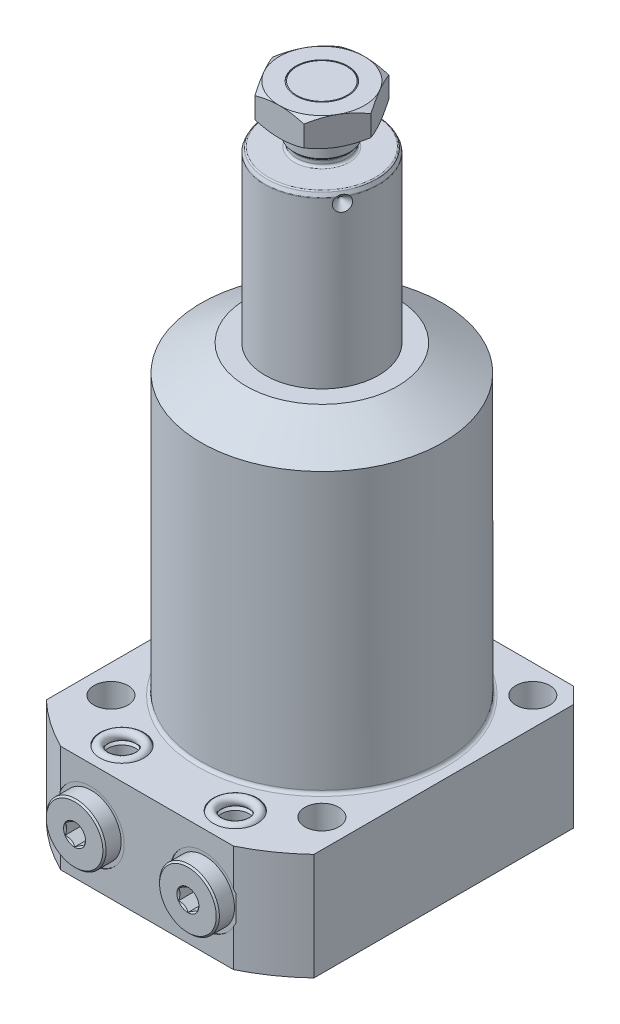
SolidWorks part; units mm, degrees
material "AISI 1020"
ref_plane "Front Plane" through (0, 0, 0) normal (0, 0, 1) x (1, 0, 0)
ref_plane "Top Plane" through (0, 0, 0) normal (0, 1, 0) x (1, 0, 0)
ref_plane "Right Plane" through (0, 0, 0) normal (1, 0, 0) x (0, 0, -1)
sketch "Sketch1" plane through (0, 0, 0) normal (0, 0, 1) x (1, 0, 0)
  line L0 (18, 0) -> (18, 149.5)
  line L1 (18, 149.5) -> (17.3005, 151)
  line L2 (17.3005, 151) -> (8, 151)
  line L3 (8, 151) -> (8, 153)
  line L4 (8, 153) -> (8.935, 153.935)
  line L5 (8.935, 153.935) -> (8.935, 168)
  line L6 (8.935, 168) -> (7.935, 169)
  line L7 (7.935, 169) -> (0, 169)
  line L8 (0, -3.075) -> (0, 64.575) construction
  line L9 (18, 0) -> (0, 0)
  line L10 (0, 0) -> (0, 169)
  line L11 (-30.3581, -34) -> (47.7767, -34) construction
  dimension "D1" = 18
  dimension "D2" = 36
  dimension "D3" = 16
  dimension "D4" = 17.87
  dimension "D5" = 203
  dimension "D6" = 25
  dimension "D7" = 1.5
  dimension "D8" = 45
  dimension "D9" = 1
  dimension "D10" = 15.065
  dimension "D11" = 7.935
  dimension "D12" = 34
revolve "Revolve2" add sketch "Sketch1" angle 360 about L8
fillet "Fillet2" radius 0.75 2 edges at (0, 151, -8) (0, 153, -8)
fillet "Fillet3" radius 0.5 2 edges at (0, 149.5, -18) (0, 151, -17.3005)
sketch "Sketch2" plane through (0, 0, 0) normal (1, 0, 0) x (0, 0, -1)
  line L0 (15.5, 147.67) -> (18, 145.17)
  line L1 (4.2016, 147.67) -> (7.575, 147.67) construction
  line L2 (16.982, 151) -> (-16.982, 151) construction
  line L3 (18, 145.17) -> (18, 147.67)
  line L4 (18, 147.67) -> (15.5, 147.67)
  line L5 (18, 0) -> (18, 149.3892) construction
  dimension "D1" = 3.33
  dimension "D2" = 45
  dimension "D3" = 5
revolve "Cut-Revolve1" cut sketch "Sketch2" angle 360 about L1
sketch "Sketch3" plane through (0, 169, 0) normal (0, 1, 0) x (1, 0, 0)
  line L1 (15.5885, 0) -> (7.7942, 13.5)
  line L2 (7.7942, 13.5) -> (-7.7942, 13.5)
  line L3 (-7.7942, 13.5) -> (-15.5885, 0)
  line L4 (-15.5885, 0) -> (-7.7942, -13.5)
  line L5 (-7.7942, -13.5) -> (7.7942, -13.5)
  line L6 (7.7942, -13.5) -> (15.5885, 0)
  circle A0 centre (0, 0) radius 13.5 construction
  circle A1 centre (0, 0) radius 8.25
  dimension "D2" = 16.5
  dimension "D1" = 27
extrude "Extrude3" add sketch "Sketch3" against normal blind 9
pattern_circular "CirPattern1" count 3 over 360 about axis through (0, -3.075, 0) along (0, -1, 0) of "Cut-Revolve1"
sketch "Sketch4" plane through (0, 0, 0) normal (1, 0, 0) x (0, 0, -1)
  line L0 (13.5, 169) -> (16.5, 169)
  line L1 (16.5, 169) -> (16.5, 167.2679)
  line L2 (16.5, 167.2679) -> (13.5, 169)
  line L3 (13.5, 164.5) -> (-10.9636, 164.5) construction
  line L4 (13.5, 160) -> (13.5, 169) construction
  line L5 (16.5, 161.7321) -> (13.5, 160)
  line L6 (16.5, 160) -> (16.5, 161.7321)
  line L7 (13.5, 160) -> (16.5, 160)
  dimension "D1" = 30
  dimension "D2" = 3
revolve "Cut-Revolve3" cut sketch "Sketch4" angle 360 about axis through (0, -3.075, 0) along (0, -1, 0)
sketch "Sketch6" plane through (0, 0, 0) normal (0, 0, 1) x (1, 0, 0)
  line L0 (0, 0) -> (0, 71.3762) construction
  line L1 (0, 97) -> (24, 97)
  line L2 (24, 97) -> (38.385, 88.6948)
  line L3 (38.385, 88.6948) -> (38.385, 0)
  line L4 (38.385, 0) -> (61.915, 0)
  line L5 (61.915, 0) -> (61.915, -34)
  line L6 (61.915, -34) -> (0, -34)
  line L7 (0, -34) -> (0, 97)
  dimension "D1" = 123.83
  dimension "D2" = 131
  dimension "D3" = 34
  dimension "D4" = 76.77
  dimension "D5" = 30
  dimension "D6" = 48
revolve "Revolve3" add sketch "Sketch6" angle 360 about L0
sketch "Sketch7" plane through (0, 0, 0) normal (0, 1, 0) x (-1, 0, 0)
  line L0 (0, 0) -> (0, -52.3237) construction
  line L1 (-42.5, 55.5) -> (42.5, 55.5)
  line L2 (-42.5, 55.5) -> (-42.5, -42.5)
  line L3 (-42.5, -42.5) -> (42.5, -42.5)
  line L4 (42.5, 55.5) -> (42.5, -42.5)
  dimension "D1" = 85
  dimension "D2" = 98
  dimension "D3" = 42.5
extrude "Cut-Extrude5" cut sketch "Sketch7" against normal through all flip side to cut
sketch "Sketch8" plane through (0, 0, 0) normal (0, 1, 0) x (-1, 0, 0)
  circle A0 centre (-33.5, 33.5) radius 5.4
  dimension "D1" = 10.8
  dimension "D2" = 33.5
  dimension "D3" = 33.5
extrude "Cut-Extrude6" cut sketch "Sketch8" against normal through all
pattern_circular "CirPattern2" count 4 over 360 about axis through (0, 0, 0) along (0, 1, 0) of "Cut-Extrude6"
chamfer "Chamfer1" distance 5 angle 45 2 edges at (-42.5, -17, -42.5) (42.5, -17, -42.5)
fillet "Fillet5" radius 1 1 edges at (0, 0, -38.385)
ref_plane "Plane1" through (0, -17, 0) normal (0, 1, 0) x (-1, 0, 0)
sketch "Sketch11" plane through (0, -17, 0) normal (0, 1, 0) x (-1, 0, 0)
  line L0 (-18, 42.9716) -> (-18, 19.7499) construction
  line L1 (-28.75, 55.5) -> (-28.75, 55.25)
  line L2 (27.4448, 55.5) -> (-27.4448, 55.5) construction
  line L3 (-28.75, 55.25) -> (-24.65, 55.25)
  line L4 (-24.65, 55.25) -> (-23.945, 54.545)
  line L5 (-23.945, 54.545) -> (-23.945, 36.53)
  line L6 (-23.945, 36.53) -> (-18, 36.53)
  line L7 (-18, 36.53) -> (-18, 55.5)
  line L8 (-18, 55.5) -> (-28.75, 55.5)
  dimension "D1" = 18
  dimension "D2" = 0.25
  dimension "D3" = 11.89
  dimension "D4" = 18.72
  dimension "D5" = 21.5
  dimension "D6" = 45
  dimension "D7" = 0.705
revolve "Cut-Revolve5" cut sketch "Sketch11" angle 360 about L0
ref_plane "Plane2" through (0, 0, 45.5) normal (0, 0, 1) x (1, 0, 0)
sketch "Sketch13" plane through (0, 0, 45.5) normal (0, 0, 1) x (1, 0, 0)
  line L0 (-22.375, -22) -> (-22.375, -31)
  line L1 (-22.375, -31) -> (-23.125, -31.75)
  line L2 (-23.125, -31.75) -> (-25, -31.75)
  line L3 (-25, -31.75) -> (-25, -34)
  line L5 (-25, -34) -> (-18, -34)
  line L6 (-18, -34) -> (-18, -22)
  line L7 (-18, -22) -> (-22.375, -22)
  line L8 (-18, 15.2099) -> (-18, -4.3918) construction
  line L9 (-27.4448, -34) -> (27.4448, -34) construction
  dimension "D1" = 18
  dimension "D2" = 8.75
  dimension "D3" = 12
  dimension "D4" = 2.25
  dimension "D5" = 14
  dimension "D6" = 45
  dimension "D7" = 0.75
revolve "Cut-Revolve6" cut sketch "Sketch13" angle 360 about L8
mirror "Mirror4" about plane through (0, -17, 0) normal (0, 1, 0) of "Cut-Revolve6"
sketch "Sketch14" plane through (0, -17, 0) normal (0, 1, 0) x (-1, 0, 0)
  line L0 (-18, 32.5881) -> (-18, 43.3353) construction
  line L1 (-18, 36.53) -> (-18, 54.545) construction
  line L2 (-21.5, 60.55) -> (-27, 60.55)
  line L3 (-27, 60.55) -> (-27.5, 60.05)
  line L4 (-27.5, 60.05) -> (-27.5, 55.25)
  line L5 (-7.25, 55.25) -> (-27.9447, 55.25) construction
  line L6 (-27.5, 55.25) -> (-23.6, 55.25)
  line L7 (-11.35, 55.25) -> (-24.65, 55.25) construction
  line L8 (-23.6, 55.25) -> (-23.6, 52.7474)
  line L9 (-23.6, 52.7474) -> (-18, 52.7474)
  line L10 (-18, 52.7474) -> (-18, 52.7484)
  line L11 (-18, 52.7484) -> (-21, 54.551)
  line L12 (-21, 54.551) -> (-21, 60.05)
  line L13 (-21, 60.05) -> (-21.5, 60.55)
  dimension "D1" = 11.2
  dimension "D2" = 2.5026
  dimension "D3" = 59
  dimension "D4" = 6
  dimension "D5" = 5.3
  dimension "D6" = 19
  dimension "D7" = 45
  dimension "D8" = 0.5
  dimension "D9" = 45
  dimension "D10" = 0.5
  dimension "D11" = 0.001
revolve "Revolve6" add sketch "Sketch14" angle 360 about L0
sketch "Sketch15" plane through (0, 0, 60.55) normal (0, 0, 1) x (1, 0, 0)
  line L1 (21, -18.7321) -> (21, -15.2679)
  line L2 (21, -15.2679) -> (18, -13.5359)
  line L3 (18, -13.5359) -> (15, -15.2679)
  line L4 (15, -15.2679) -> (15, -18.7321)
  line L5 (15, -18.7321) -> (18, -20.4641)
  line L6 (18, -20.4641) -> (21, -18.7321)
  circle A0 centre (18, -17) radius 3 construction
  dimension "D1" = 6
extrude "Cut-Extrude8" cut sketch "Sketch15" against normal blind 5.3
mirror "Mirror1" about plane through (0, 0, 0) normal (1, 0, 0) of "Mirror4", "Cut-Extrude8", "Revolve6", "Cut-Revolve6", "Cut-Revolve5"
sketch "Sketch16" plane through (0, 0, 45.5) normal (0, 0, 1) x (1, 0, 0)
  line L1 (-18, 9.3219) -> (-18, -15.1063) construction
  line L2 (-18, -31) -> (-18, -22) construction
  line L3 (-27.4448, 0) -> (27.4448, 0) construction
  circle A0 centre (-23.5, -0.75) radius 1.5
  dimension "D1" = 3
  dimension "D3" = 0.75
  dimension "D2" = 11
revolve "Revolve7" add sketch "Sketch16" angle 360 about L1
mirror "Mirror3" about plane through (0, 0, 0) normal (1, 0, 0) of bodies 128
mirror "Mirror5" about plane through (0, -17, 0) normal (0, 1, 0) of bodies 128 130
